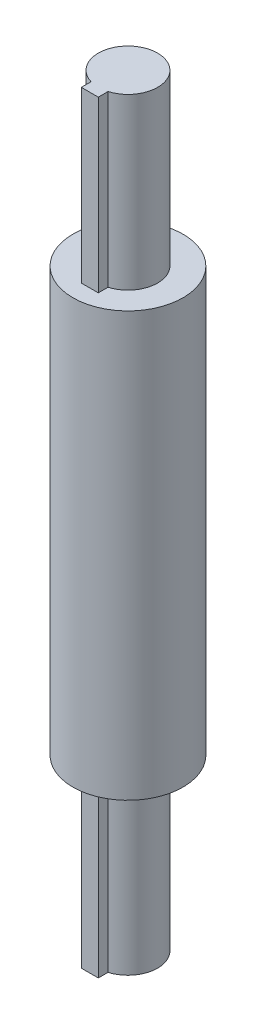
SolidWorks part; units mm, degrees
ref_plane "Front Plane" through (0, 0, 0) normal (0, 0, 1) x (1, 0, 0)
ref_plane "Top Plane" through (0, 0, 0) normal (0, 1, 0) x (1, 0, 0)
ref_plane "Right Plane" through (0, 0, 0) normal (1, 0, 0) x (0, 0, -1)
sketch "Sketch1" plane through (0, 0, 0) normal (0, 1, 0) x (1, 0, 0)
  circle A0 centre (0, 0) radius 3.25
  dimension "D1" = 6.5
extrude "Boss-Extrude1" add sketch "Sketch1" along normal blind 25
sketch "Sketch2" plane through (0, 25, 0) normal (0, 1, 0) x (1, 0, 0)
  circle A0 centre (0, 0) radius 1.75
  dimension "D1" = 3.5
extrude "Boss-Extrude2" add sketch "Sketch2" along normal blind 10 and the other way blind 35
sketch "Sketch3" plane through (0, -10, 0) normal (0, -1, 0) x (1, 0, 0)
  line L1 (-0.5, 1.25) -> (0.5, 1.25)
  line L2 (-0.5, 1.25) -> (-0.5, 2.25)
  line L3 (-0.5, 2.25) -> (0.5, 2.25)
  line L4 (0.5, 1.25) -> (0.5, 2.25)
  line L5 (-0.5, 1.25) -> (0.5, 2.25) construction
  line L6 (-0.5, 2.25) -> (0.5, 1.25) construction
  circle A0 centre (0, 0) radius 1.75 construction
  point P0 (0, 1.75)
  point P7 (0.4983, 1.6775)
  dimension "D1" = 1
  dimension "D2" = 1
extrude "Boss-Extrude3" add sketch "Sketch3" against normal through all
